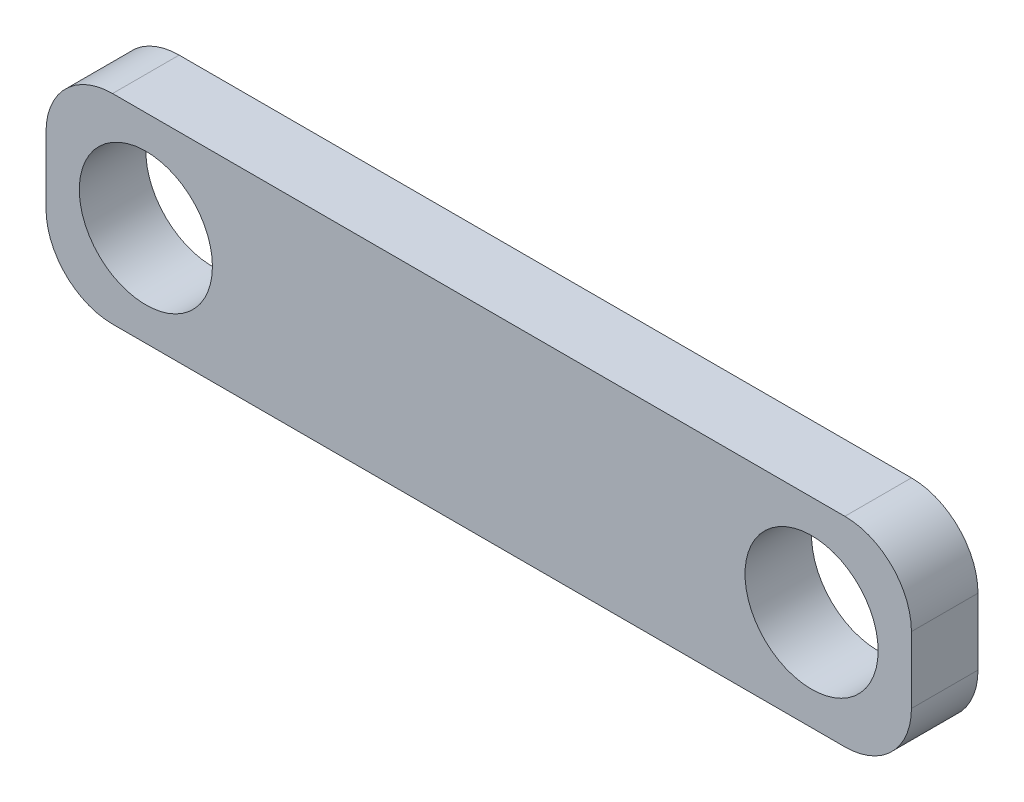
SolidWorks part; units mm, degrees
ref_plane "Alzado" through (0, 0, 0) normal (0, 0, 1) x (1, 0, 0)
ref_plane "Planta" through (0, 0, 0) normal (0, 1, 0) x (1, 0, 0)
ref_plane "Vista lateral" through (0, 0, 0) normal (1, 0, 0) x (0, 0, -1)
sketch "Croquis1" plane through (0, 0, 0) normal (0, 0, 1) x (1, 0, 0)
  line L1 (-55, 15) -> (55, 15)
  line L2 (-65, 5) -> (-65, -5)
  line L3 (-55, -15) -> (55, -15)
  line L4 (65, 5) -> (65, -5)
  line L5 (-65, 15) -> (65, -15) construction
  line L6 (-65, -15) -> (65, 15) construction
  circle A0 centre (-50, 0) radius 10
  arc A1 (55, 15) -> (65, 5) centre (55, 5) cw
  arc A2 (65, -5) -> (55, -15) centre (55, -5) cw
  arc A3 (-55, -15) -> (-65, -5) centre (-55, -5) cw
  arc A4 (-55, 15) -> (-65, 5) centre (-55, 5) ccw
  circle A5 centre (50, 0) radius 10
  point P0 (0, 0)
  dimension "D1" = 130
  dimension "D2" = 10
  dimension "D3" = 50
  dimension "D4" = 50
extrude "Saliente-Extruir1" add sketch "Croquis1" along normal mid plane 10 from offset 0
